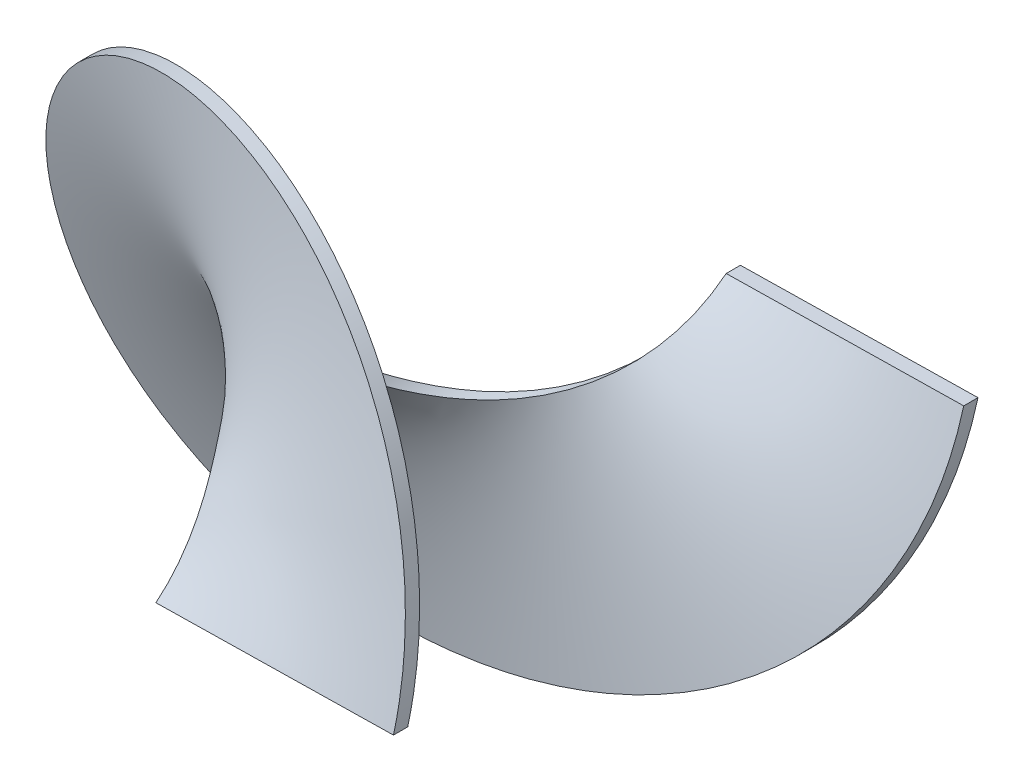
SolidWorks part; units mm, degrees
ref_plane "Front Plane" through (0, 0, 0) normal (0, 0, 1) x (1, 0, 0)
ref_plane "Top Plane" through (0, 0, 0) normal (0, 1, 0) x (1, 0, 0)
ref_plane "Right Plane" through (0, 0, 0) normal (1, 0, 0) x (0, 0, -1)
sketch "Skica1" plane through (0, 0, 0) normal (0, 0, 1) x (1, 0, 0)
  circle A0 centre (0, 0) radius 15
  dimension "D1" = 30
curve "Šroubovice/spirála1" pitch 120 height 120 turns 1
sketch "Skica2" plane through (0, 0, 0) normal (0, 1, 0) x (1, 0, 0)
  line L1 (14.9977, 0) -> (64.9977, 0)
  line L2 (14.9977, 0) -> (14.9977, 3)
  line L3 (14.9977, 3) -> (64.9977, 3)
  line L4 (64.9977, 0) -> (64.9977, 3)
  spline S0 degree 3 poles (14.9977, 0) (15.0238, -1.9021) (14.6252, -5.7155) (12.7276, -11.4282) (9.6992, -17.1429) (5.809, -22.8571) (1.4026, -28.5714) (-3.1284, -34.2857) (-7.3815, -40) (-10.9786, -45.7143) (-13.6003, -51.4286) (-15.0135, -57.1429) (-15.0927, -62.8571) (-13.8309, -68.5714) (-11.3401, -74.2857) (-7.8417, -80) (-3.6465, -85.7143) (0.8726, -91.4286) (5.3143, -97.1429) (9.2837, -102.8571) (12.4283, -108.5718) (14.4685, -114.2845) (14.9716, -118.0979) (14.9977, -120) knots 0 0 0 0 0.047619 0.095238 0.142857 0.190476 0.238095 0.285714 0.333333 0.380952 0.428571 0.47619 0.52381 0.571429 0.619048 0.666667 0.714286 0.761905 0.809524 0.857143 0.904762 0.952381 1 1 1 1 construction
  dimension "D1" = 50
  dimension "D2" = 3
sweep "Táhnout po křivce1" add profiles "Skica2" path "Šroubovice/spirála1"
